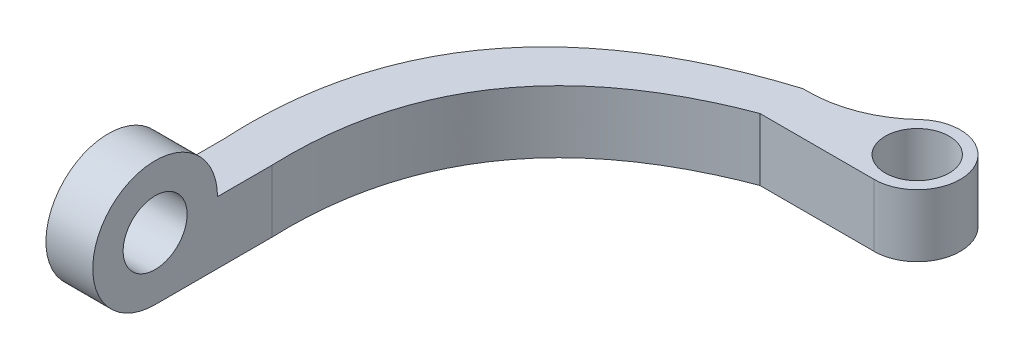
SolidWorks part; units mm, degrees
ref_plane "Plano frontal" through (0, 0, 0) normal (0, 0, 1) x (1, 0, 0)
ref_plane "Plano superior" through (0, 0, 0) normal (0, 1, 0) x (1, 0, 0)
ref_plane "Plano direito" through (0, 0, 0) normal (1, 0, 0) x (0, 0, -1)
sketch "Esboço1" plane through (0, 0, 0) normal (0, 1, 0) x (1, 0, 0)
  line L0 (-8.4551, 52.0129) -> (6.1983, 52.0129)
  line L1 (-40, 0) -> (-34, 0)
  line L2 (-40, 0) -> (-40, 15)
  line L3 (6.1983, 57.5284) -> (6.1983, 52.0129)
  line L4 (5.0172, 54.7707) -> (-57.3168, 54.7707) construction
  line L5 (-34, 0) -> (-34, 15)
  line L6 (-8.4551, 57.5284) -> (6.1983, 57.5284)
  spline S0 degree 2 poles (-34, 15) (-35.043, 42.0402) (-8.4551, 52.0129) knots 0 0 0 1 1 1
  spline S1 degree 2 poles (-40, 15) (-41.8065, 47.1706) (-8.4551, 57.5284) knots 0 0 0 1 1 1
  point P0 (5.0172, 54.7707)
  point P1 (0, 0)
  point P8 (-74, 52)
  dimension "D6" = 15
  dimension "D1" = 55
  dimension "D3" = 6
  dimension "D4" = 15
  dimension "D5" = 3
extrude "Ressalto-extrusão4" add sketch "Esboço1" along normal blind 8
sketch "Esboço7" plane through (-34, 0, 0) normal (1, 0, 0) x (0, 0, -1)
  circle A0 centre (0, 8) radius 4.1
extrude "Corte-extrusão3" cut sketch "Esboço7" against normal blind 8
sketch "Esboço8" plane through (-34, 0, 0) normal (1, 0, 0) x (0, 0, -1)
  circle A0 centre (0, 8) radius 8
  circle A1 centre (0, 8) radius 4.1
extrude "Ressalto-extrusão5" add sketch "Esboço8" against normal blind 6
sketch "Esboço14" plane through (0, 8, 0) normal (0, 1, 0) x (1, 0, 0)
  circle A0 centre (6.1983, 57.5284) radius 4.1
  circle A1 centre (6.1983, 57.5284) radius 5.5155
extrude "Ressalto-extrusão8" add sketch "Esboço14" against normal blind 8
fillet "Filete3" radius 15 1 edges at (0.6828, 4, -57.5284)
sketch "Esboço15" plane through (0, 8, 0) normal (0, 1, 0) x (1, 0, 0)
  line L0 (6.1983, 57.5284) -> (2.0983, 57.5284) construction
  line L1 (6.1983, 57.5284) -> (2.0983, 57.5284)
  line L2 (6.1983, 53.4284) -> (6.1983, 57.5284) construction
  line L3 (6.1983, 53.4284) -> (6.1983, 57.5284)
  arc A2 (2.0983, 57.5284) -> (6.1983, 53.4284) centre (6.1983, 57.5284) ccw
extrude "Corte-extrusão6" cut sketch "Esboço15" against normal blind 8 contours L1 A2 L3
